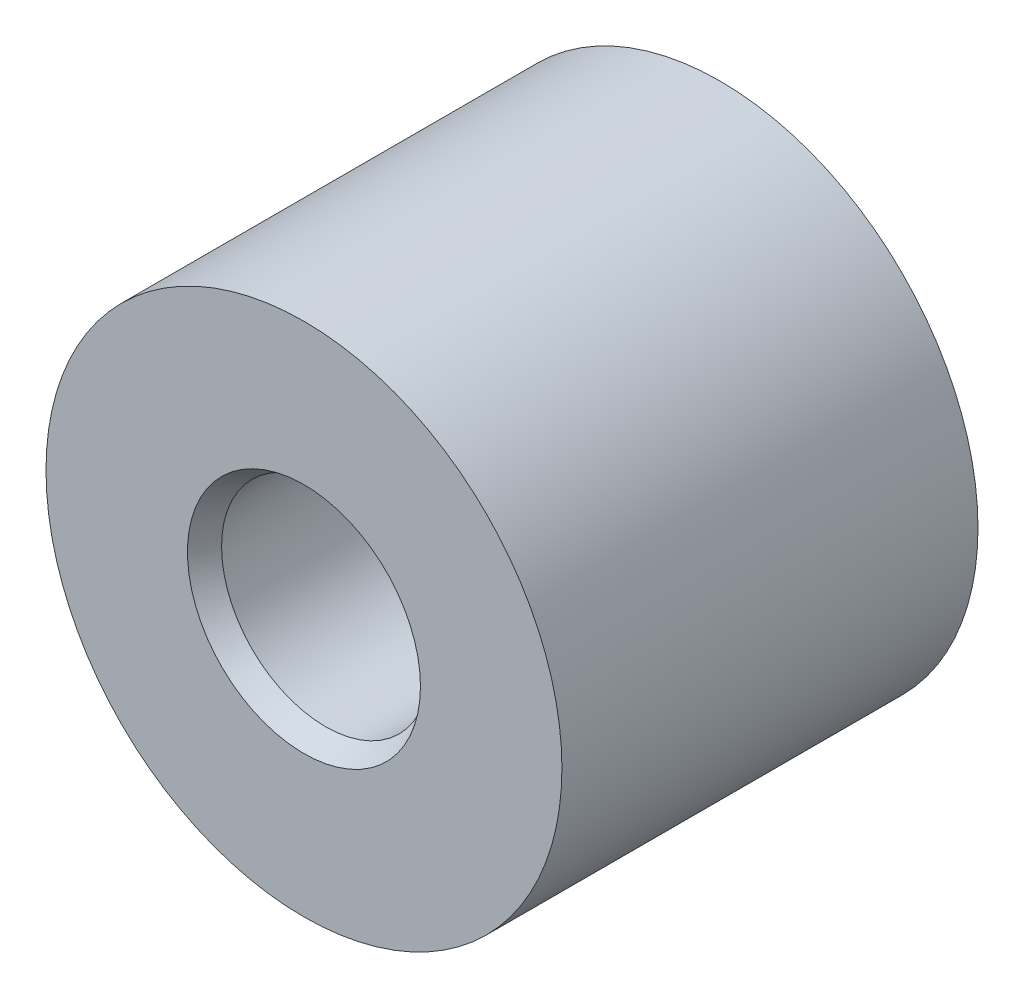
SolidWorks part; units mm, degrees
ref_plane "Front Plane" through (0, 0, 0) normal (0, 0, 1) x (1, 0, 0)
ref_plane "Top Plane" through (0, 0, 0) normal (0, 1, 0) x (1, 0, 0)
ref_plane "Right Plane" through (0, 0, 0) normal (1, 0, 0) x (0, 0, -1)
sketch "Sketch2" plane through (0, 0, 0) normal (0, 0, 1) x (1, 0, 0)
  circle A0 centre (0, 0) radius 3.1
  dimension "D1" = 6.2
extrude "Boss-Extrude1" add sketch "Sketch2" against normal blind 5
hole_wizard "Ø2.5 (2.5) Diameter Hole1" positions "Sketch5" profile "Sketch4" hole size "Ø2.5" standard "DIN" end condition up to next
sketch "Sketch5" plane through (0, 0, 0) normal (0, 0, 1) x (1, 0, 0)
  point P0 (0, 0)
sketch "Sketch4" plane through (0, 0, 0) normal (1, 0, 0) x (0, -1, 0)
  line L0 (0, 0) -> (0, 5)
  line L1 (0, 5) -> (1.25, 5)
  line L2 (1.25, 5) -> (1.25, 0.2598)
  line L3 (1.25, 0.2598) -> (1.4, 0)
  line L5 (1.4, 0) -> (0, 0)
  line L6 (-1.25, 0.2598) -> (-1.4, 0) construction
  line L11 (0, -6.35) -> (0, 107.95) construction
  dimension "Thru Hole Dia." = 2.5
  dimension "Thru Hole Depth" = 5
  dimension "Near C'Sink Dia." = 2.8
  dimension "Near C'Sink Angle" = 60
